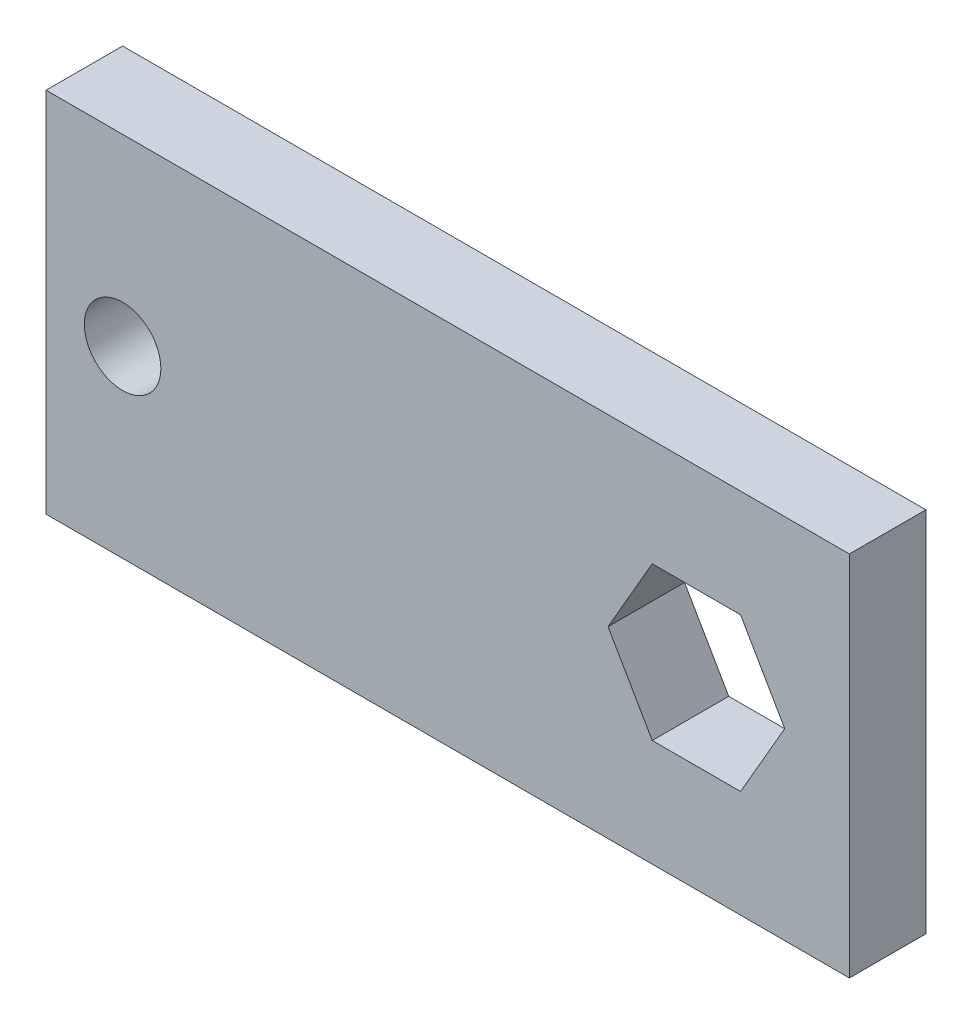
SolidWorks part; units mm, degrees
ref_plane "Front" through (0, 0, 0) normal (0, 0, 1) x (1, 0, 0)
ref_plane "Top" through (0, 0, 0) normal (0, 1, 0) x (1, 0, 0)
ref_plane "Right" through (0, 0, 0) normal (1, 0, 0) x (0, 0, -1)
sketch "Sketch2" plane through (0, 0, 0) normal (0, 0, 1) x (1, 0, 0)
  line L0 (12.7, 15.24) -> (12.7, -15.24)
  line L1 (3.6662, 6.35) -> (-3.6662, 6.35)
  line L2 (-3.6662, 6.35) -> (-7.3323, 0)
  line L3 (-7.3323, 0) -> (-3.6662, -6.35)
  line L4 (-3.6662, -6.35) -> (3.6662, -6.35)
  line L5 (3.6662, -6.35) -> (7.3323, 0)
  line L6 (7.3323, 0) -> (3.6662, 6.35)
  line L7 (12.7, 15.24) -> (-53.975, 15.24)
  line L8 (12.7, -15.24) -> (-53.975, -15.24)
  line L9 (-53.975, 15.24) -> (-53.975, -15.24)
  line L10 (-53.975, 0) -> (12.7, 0) construction
  circle A1 centre (-47.625, 0) radius 3.175
  circle A4 centre (0, 0) radius 6.35 construction
  dimension "D1" = 6.35
  dimension "D2" = 6.35
  dimension "D4" = 12.7
  dimension "D5" = 66.675
  dimension "D6" = 30.48
  dimension "D7" = 12.7
extrude "Boss-Extrude2" add sketch "Sketch2" along normal blind 6.35
